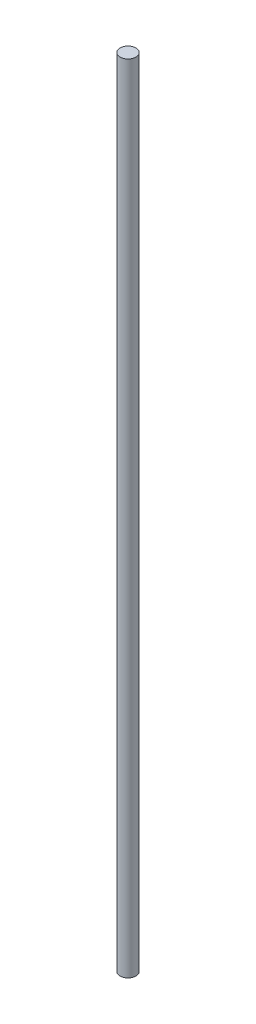
SolidWorks part; units mm, degrees
ref_plane "Alzado" through (0, 0, 0) normal (0, 0, 1) x (1, 0, 0)
ref_plane "Planta" through (0, 0, 0) normal (0, 1, 0) x (1, 0, 0)
ref_plane "Vista lateral" through (0, 0, 0) normal (1, 0, 0) x (0, 0, -1)
sketch "Croquis1" plane through (0, 0, 0) normal (0, 0, 1) x (1, 0, 0)
  line L0 (0, 0) -> (0, 400)
  dimension "D1" = 400
sketch "Croquis2" plane through (0, 0, 0) normal (0, 1, 0) x (1, 0, 0)
  circle A0 centre (0, 0) radius 4
sweep "Barrer1" add profiles "Croquis2" path "Croquis1"
